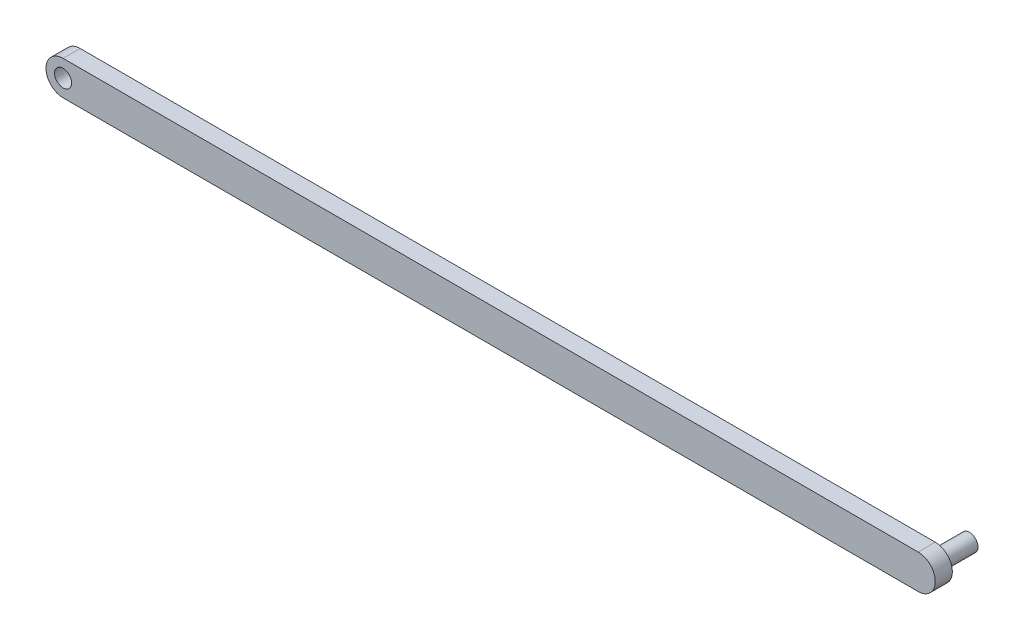
SolidWorks part; units mm, degrees
ref_plane "前视基准面" through (0, 0, 0) normal (0, 0, 1) x (1, 0, 0)
ref_plane "上视基准面" through (0, 0, 0) normal (0, 1, 0) x (1, 0, 0)
ref_plane "右视基准面" through (0, 0, 0) normal (1, 0, 0) x (0, 0, -1)
sketch "草图1" plane through (0, 0, 0) normal (0, 0, 1) x (1, 0, 0)
  line L1 (-59.14, -2) -> (40.86, -2)
  line L2 (-59.14, 2) -> (40.86, 2)
  arc A0 (40.86, -2) -> (40.86, 2) centre (40.86, 0) ccw
  arc A1 (-59.14, 2) -> (-59.14, -2) centre (-59.14, 0) ccw
  dimension "D1" = 100
extrude "凸台-拉伸1" add sketch "草图1" along normal blind 2
sketch "草图2" plane through (0, 0, 0) normal (0, 0, -1) x (-1, 0, 0)
  circle A0 centre (-40.86, 0) radius 1
extrude "凸台-拉伸2" add sketch "草图2" along normal blind 4
sketch "草图3" plane through (0, 0, 0) normal (0, 0, -1) x (-1, 0, 0)
  circle A0 centre (59.14, 0) radius 1
extrude "切除-拉伸1" cut sketch "草图3" against normal blind 4
